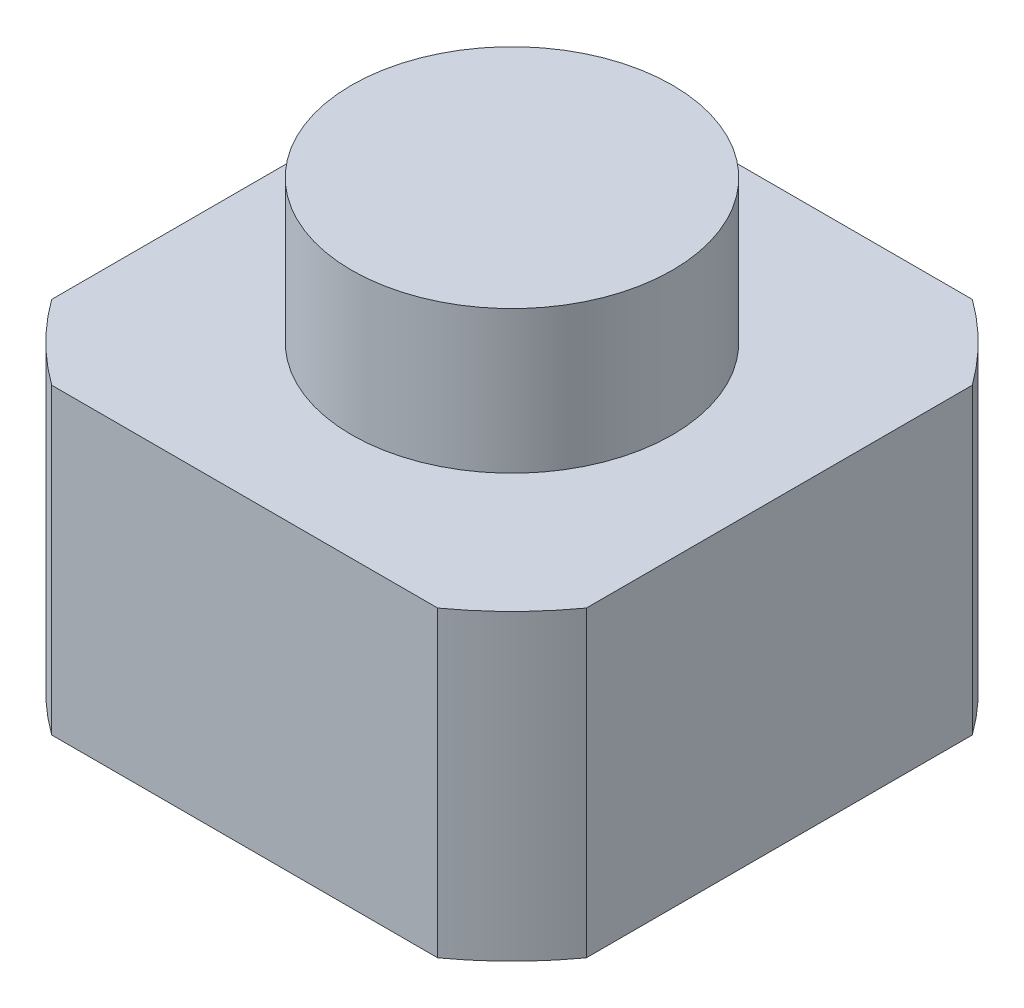
SolidWorks part; units mm, degrees
ref_plane "Front Plane" through (0, 0, 0) normal (0, 0, 1) x (1, 0, 0)
ref_plane "Top Plane" through (0, 0, 0) normal (0, 1, 0) x (1, 0, 0)
ref_plane "Right Plane" through (0, 0, 0) normal (1, 0, 0) x (0, 0, -1)
sketch "Sketch2" plane through (0, 0, 0) normal (0, 1, 0) x (1, 0, 0)
  line L1 (-2.1656, -3) -> (2.1656, -3)
  line L2 (-3, -2.1656) -> (-3, 2.1656)
  line L3 (-2.1656, 3) -> (2.1656, 3)
  line L4 (3, -2.1656) -> (3, 2.1656)
  arc A0 (-2.1656, 3) -> (-3, 2.1656) centre (0, 0) ccw
  arc A1 (-3, -2.1656) -> (-2.1656, -3) centre (0, 0) ccw
  arc A2 (3, 2.1656) -> (2.1656, 3) centre (0, 0) ccw
  arc A3 (2.1656, -3) -> (3, -2.1656) centre (0, 0) ccw
  dimension "D1" = 7.4
  dimension "D2" = 6
extrude "Boss-Extrude1" add sketch "Sketch2" along normal blind 3.4
sketch "Sketch3" plane through (0, 3.4, 0) normal (0, 1, 0) x (1, 0, 0)
  circle A0 centre (0, 0) radius 1.8
  dimension "D1" = 3.6
extrude "Boss-Extrude2" add sketch "Sketch3" along normal offset from surface (1.6 mm away) 5 up to face at (0, 0, 0)
